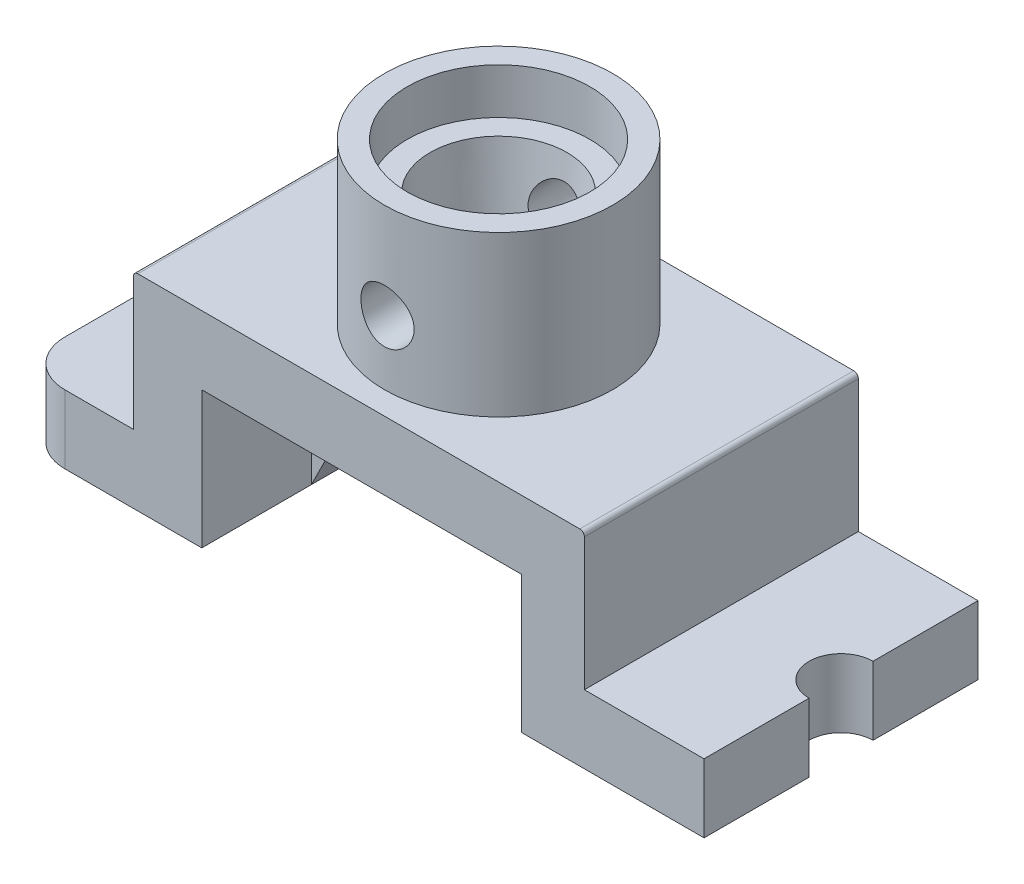
SolidWorks part; units mm, degrees
ref_plane "Front Plane" through (0, 0, 0) normal (0, 0, 1) x (1, 0, 0)
ref_plane "Top Plane" through (0, 0, 0) normal (0, 1, 0) x (1, 0, 0)
ref_plane "Right Plane" through (0, 0, 0) normal (1, 0, 0) x (0, 0, -1)
sketch "Sketch1" plane through (0, 0, 0) normal (0, 0, 1) x (1, 0, 0)
  line L0 (-175.8621, 0) -> (-575.8621, 0)
  line L1 (-575.8621, 0) -> (-575.8621, 150)
  line L2 (-575.8621, 150) -> (-325.8621, 150)
  line L3 (-325.8621, 150) -> (-325.8621, 450)
  line L4 (-325.8621, 450) -> (662.069, 450)
  line L5 (662.069, 450) -> (662.069, 150)
  line L6 (662.069, 150) -> (924.1379, 150)
  line L7 (924.1379, 150) -> (924.1379, 0)
  line L8 (924.1379, 0) -> (524.1379, 0)
  line L9 (524.1379, 0) -> (524.1379, 300)
  line L10 (524.1379, 300) -> (-175.8621, 300)
  line L11 (-175.8621, 300) -> (-175.8621, 0)
  dimension "D1" = 150
  dimension "D2" = 150
  dimension "D3" = 400
  dimension "D4" = 400
  dimension "D5" = 700
  dimension "D6" = 1100
  dimension "D7" = 150
  dimension "D8" = 450
  dimension "D9" = 150
  dimension "D10" = 250
  dimension "D11" = 262.069
extrude "Boss-Extrude1" add sketch "Sketch1" along normal blind 600
sketch "Sketch2" plane through (0, 450, 0) normal (0, 1, 0) x (1, 0, 0)
  line L0 (662.069, 0) -> (-325.8621, 0) construction
  line L1 (662.069, -600) -> (-325.8621, -600) construction
  line L2 (924.1379, -600) -> (924.1379, 0) construction
  circle A1 centre (174.1379, -300) radius 250
  dimension "D3" = 500
  dimension "D1" = 750
  dimension "D2" = 300
extrude "Boss-Extrude3" add sketch "Sketch2" along normal blind 350
sketch "Sketch6" plane through (0, 800, 0) normal (0, 1, 0) x (1, 0, 0)
  circle A0 centre (174.1379, -300) radius 200
extrude "Cut-Extrude1" cut sketch "Sketch6" against normal blind 100
sketch "Sketch7" plane through (0, 700, 0) normal (0, 1, 0) x (1, 0, 0)
  circle A0 centre (174.1379, -300) radius 150
  dimension "D1" = 300
sketch "Sketch8" plane through (0, 300, 0) normal (0, -1, 0) x (1, 0, 0)
  circle A0 centre (174.1379, 300) radius 100
  dimension "D1" = 200
loft "Cut-Loft1" cut profiles "Sketch8", "Sketch7"
sketch "Sketch9" plane through (0, 150, 0) normal (0, 1, 0) x (1, 0, 0)
  line L1 (-325.8621, -600) -> (-575.8621, -600) construction
  line L2 (-575.8621, -600) -> (-575.8621, 0) construction
  line L3 (-325.8621, 0) -> (-575.8621, 0) construction
  circle A0 centre (-450.8621, -450) radius 60
  circle A1 centre (-450.8621, -150) radius 60
  dimension "D1" = 120
  dimension "D2" = 120
  dimension "D3" = 125
  dimension "D4" = 125
  dimension "D5" = 150
  dimension "D6" = 150
fillet "Fillet2" radius 100 2 edges at (-575.8621, 75, 0) (-575.8621, 75, 600)
fillet "Fillet3" radius 10 2 edges at (662.069, 450, 300) (-325.8621, 450, 300)
sketch "Sketch11" plane through (0, 0, 0) normal (0, 0, 1) x (1, 0, 0)
  line L0 (374.1379, 800) -> (-25.8621, 800) construction
  line L1 (424.1379, 450) -> (424.1379, 800) construction
  circle A0 centre (174.1379, 590) radius 58.2358
  dimension "D2" = 250
  dimension "D1" = 210
extrude "Cut-Extrude5" cut sketch "Sketch11" along normal through all both and the other way through all
sketch "Sketch12" plane through (0, 150, 0) normal (0, 1, 0) x (1, 0, 0)
  line L0 (924.1379, -600) -> (924.1379, 0) construction
  circle A0 centre (924.1379, -300) radius 70
  dimension "D1" = 140
extrude "Cut-Extrude6" cut sketch "Sketch12" against normal up to next
ref_plane "Plane1" through (0, 0, 300) normal (0, 0, 1) x (1, 0, 0)
sketch "Sketch13" plane through (0, 0, 300) normal (0, 0, 1) x (1, 0, 0)
  line L0 (-175.8621, 0) -> (-25.8621, 300)
  line L1 (-175.8621, 300) -> (524.1379, 300) construction
  dimension "D1" = 150
rib "Rib1" sketch "Sketch13" sketch "Sketch13" thickness 120 extrusion direction parallel to sketch draft on no parameters "D1"=120
sketch "Sketch14" plane through (0, 0, 300) normal (0, 0, 1) x (1, 0, 0)
  line L0 (524.1379, 0) -> (374.1379, 300)
  line L1 (-175.8621, 300) -> (524.1379, 300) construction
  dimension "1" = 150
rib "Rib2" sketch "Sketch14" sketch "Sketch14" thickness 120 extrusion direction parallel to sketch draft on no parameters "D1"=120
